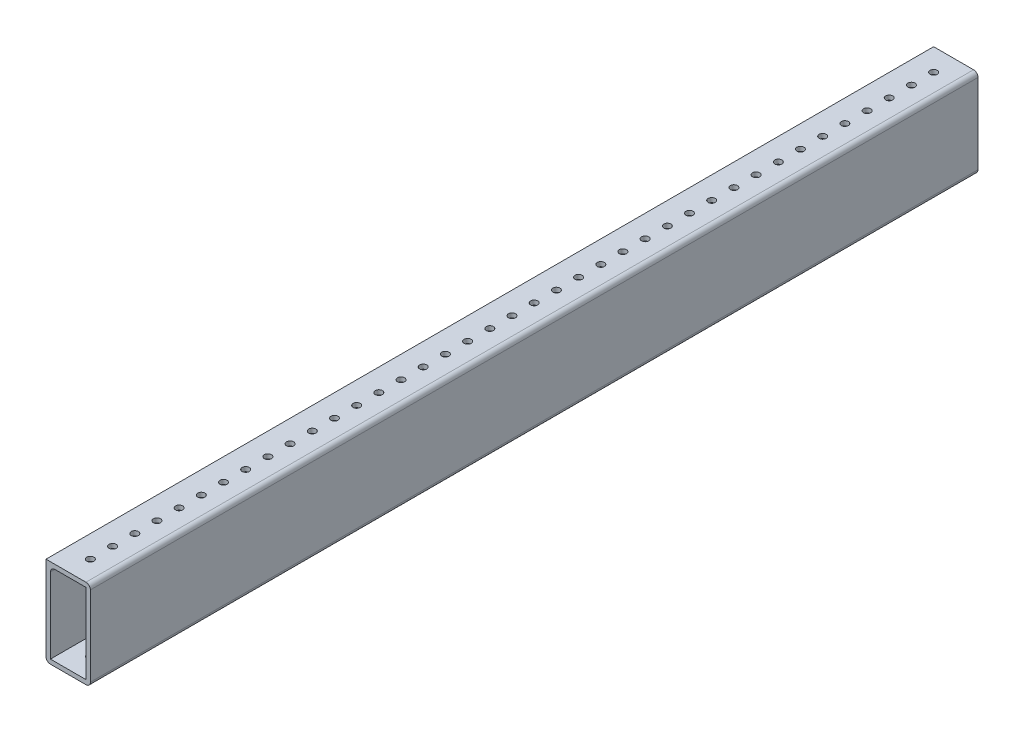
SolidWorks part; units mm, degrees
ref_plane "Front Plane" through (0, 0, 0) normal (0, 0, 1) x (1, 0, 0)
ref_plane "Top Plane" through (0, 0, 0) normal (0, 1, 0) x (1, 0, 0)
ref_plane "Right Plane" through (0, 0, 0) normal (1, 0, 0) x (0, 0, -1)
sketch "Sketch1" plane through (0, 0, 0) normal (0, 0, 1) x (1, 0, 0)
  line L0 (2.54, 2.54) -> (2.54, 48.26)
  line L1 (0, 0) -> (25.4, 0)
  line L2 (0, 0) -> (0, 50.8)
  line L3 (0, 50.8) -> (25.4, 50.8)
  line L4 (25.4, 0) -> (25.4, 50.8)
  line L5 (2.54, 48.26) -> (22.86, 48.26)
  line L6 (22.86, 2.54) -> (22.86, 48.26)
  line L7 (2.54, 2.54) -> (22.86, 2.54)
  dimension "D1" = 50.8
  dimension "D2" = 25.4
  dimension "D3" = 2.54
extrude "Boss-Extrude1" add sketch "Sketch1" along normal blind 508
sketch "Sketch2" plane through (0, 50.8, 0) normal (0, 1, 0) x (1, 0, 0)
  line L0 (0, -508) -> (0, 0) construction
  line L1 (25.4, 0) -> (0, 0) construction
  circle A0 centre (12.7, -12.7) radius 2.032
  circle A1 centre (12.7, -25.4) radius 2.032
  circle A2 centre (12.7, -38.1) radius 2.032
  circle A3 centre (12.7, -50.8) radius 2.032
  circle A4 centre (12.7, -63.5) radius 2.032
  circle A5 centre (12.7, -76.2) radius 2.032
  circle A6 centre (12.7, -88.9) radius 2.032
  circle A7 centre (12.7, -101.6) radius 2.032
  circle A8 centre (12.7, -114.3) radius 2.032
  circle A9 centre (12.7, -127) radius 2.032
  circle A10 centre (12.7, -139.7) radius 2.032
  circle A11 centre (12.7, -152.4) radius 2.032
  circle A12 centre (12.7, -165.1) radius 2.032
  circle A13 centre (12.7, -177.8) radius 2.032
  circle A14 centre (12.7, -190.5) radius 2.032
  circle A15 centre (12.7, -203.2) radius 2.032
  circle A16 centre (12.7, -215.9) radius 2.032
  circle A17 centre (12.7, -228.6) radius 2.032
  circle A18 centre (12.7, -241.3) radius 2.032
  circle A19 centre (12.7, -254) radius 2.032
  circle A20 centre (12.7, -266.7) radius 2.032
  circle A21 centre (12.7, -279.4) radius 2.032
  circle A22 centre (12.7, -292.1) radius 2.032
  circle A23 centre (12.7, -304.8) radius 2.032
  circle A24 centre (12.7, -317.5) radius 2.032
  circle A25 centre (12.7, -330.2) radius 2.032
  circle A26 centre (12.7, -342.9) radius 2.032
  circle A27 centre (12.7, -355.6) radius 2.032
  circle A28 centre (12.7, -368.3) radius 2.032
  circle A29 centre (12.7, -381) radius 2.032
  circle A30 centre (12.7, -393.7) radius 2.032
  circle A31 centre (12.7, -406.4) radius 2.032
  circle A32 centre (12.7, -419.1) radius 2.032
  circle A33 centre (12.7, -431.8) radius 2.032
  circle A34 centre (12.7, -444.5) radius 2.032
  circle A35 centre (12.7, -457.2) radius 2.032
  circle A36 centre (12.7, -469.9) radius 2.032
  circle A37 centre (12.7, -482.6) radius 2.032
  circle A38 centre (12.7, -495.3) radius 2.032
  dimension "D1" = 4.064
  dimension "D2" = 12.7
  dimension "D3" = 12.7
  dimension "D5" = 12.7
  dimension "D4" = 39
extrude "Cut-Extrude1" cut sketch "Sketch2" against normal blind 508
fillet "Fillet1" radius 2.54 4 edges at (25.4, 0, 254) (0, 0, 254) (2.54, 48.26, 254) (25.4, 50.8, 254)
